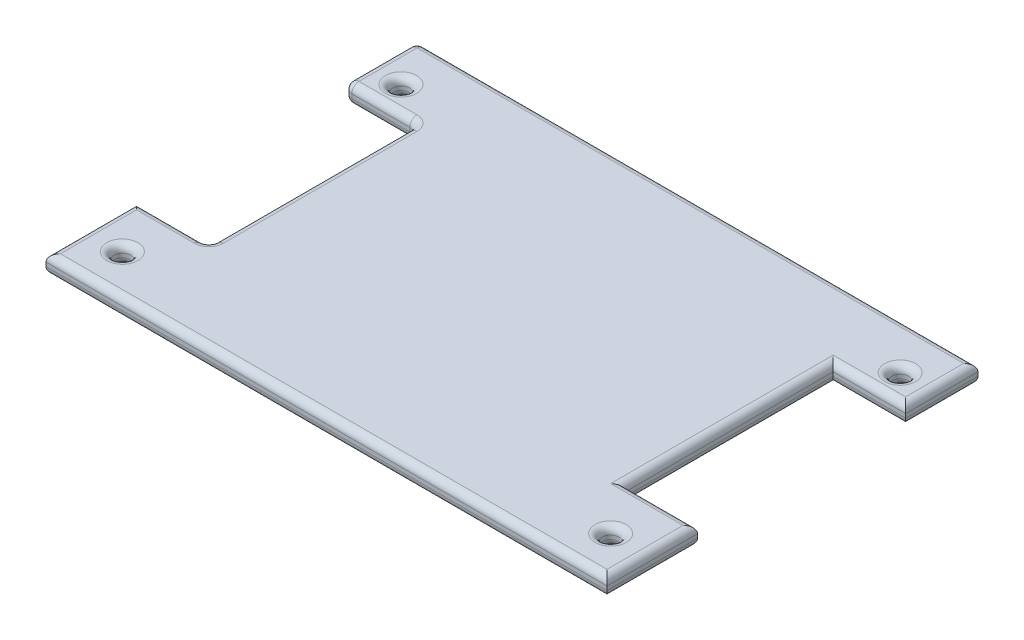
SolidWorks part; units mm, degrees
ref_plane "Front Plane" through (0, 0, 0) normal (0, 0, 1) x (1, 0, 0)
ref_plane "Top Plane" through (0, 0, 0) normal (0, 1, 0) x (1, 0, 0)
ref_plane "Right Plane" through (0, 0, 0) normal (1, 0, 0) x (0, 0, -1)
sketch "Sketch1" plane through (0, 0, 0) normal (0, 1, 0) x (1, 0, 0)
  line L0 (77.5, 0) -> (-77.5, 0)
  line L1 (0, 0) -> (0, 102.5)
  line L2 (77.5, 102.5) -> (-77.5, 102.5)
  line L3 (-77.5, 102.5) -> (-77.5, 82.5)
  line L4 (-77.5, 82.5) -> (-57.5, 82.5)
  line L5 (-57.5, 82.5) -> (-57.5, 25)
  line L6 (-57.5, 25) -> (-77.5, 25)
  line L7 (-77.5, 25) -> (-77.5, 0)
  line L8 (77.5, 25) -> (77.5, 0)
  line L9 (57.5, 25) -> (77.5, 25)
  line L10 (57.5, 82.5) -> (57.5, 25)
  line L11 (77.5, 82.5) -> (57.5, 82.5)
  line L12 (77.5, 102.5) -> (77.5, 82.5)
  dimension "D1" = 77.5
  dimension "D2" = 20
  dimension "D3" = 25
  dimension "D4" = 57.5
  dimension "D5" = 20
  dimension "20" = 20
extrude "Boss-Extrude1" add sketch "Sketch1" along normal blind 5.08 contours L6 L7 L0 L1 L2 L3 L4 L5 | L12 L2 L1 L0 L8 L9 L10 L11
sketch "Sketch2" plane through (0, 5.08, 0) normal (0, 1, 0) x (1, 0, 0)
  line L0 (-77.5, 102.5) -> (-77.5, 82.5) construction
  line L1 (77.5, 0) -> (-77.5, 0) construction
  line L2 (77.5, 102.5) -> (77.5, 82.5) construction
  line L3 (-77.5, 25) -> (-77.5, 0) construction
  line L4 (77.5, 25) -> (77.5, 0) construction
  circle A0 centre (-68.95, 89.55) radius 2.3
  circle A1 centre (68.95, 89.55) radius 2.3
  circle A2 centre (-67.45, 11.05) radius 2.3
  circle A3 centre (67.45, 11.05) radius 2.3
  dimension "D3" = 4.6
  dimension "D4" = 4.6
  dimension "D7" = 4.6
  dimension "D8" = 4.6
  dimension "D1" = 8.55
  dimension "D2" = 89.55
  dimension "D5" = 8.55
  dimension "D6" = 89.55
  dimension "D9" = 11.05
  dimension "D10" = 10.05
  dimension "D11" = 10.05
  dimension "D12" = 11.05
extrude "Cut-Extrude1" cut sketch "Sketch2" against normal up to surface (5.08 mm away) up to face at (0, 0, -52.9167)
fillet "Fillet1" radius 2 36 edges at (-77.5, 0, -12.5) (0, 0, 0) (77.5, 0, -12.5) (67.5, 0, -25) (57.5, 0, -53.75) (67.5, 0, -82.5) (77.5, 0, -92.5) (0, 0, -102.5) (-67.5, 0, -82.5) (-67.5, 0, -25) (-68.95, 0, -87.25) (67.45, 0, -8.75) (-67.45, 0, -8.75) (68.95, 0, -87.25) (-67.5, 5.08, -82.5) (0, 5.08, -102.5) (77.5, 5.08, -92.5) (67.5, 5.08, -82.5) (57.5, 5.08, -53.75) (67.5, 5.08, -25) (77.5, 5.08, -12.5) (0, 5.08, 0) (-77.5, 5.08, -12.5) (-67.5, 5.08, -25) (-68.95, 5.08, -87.25) (67.45, 5.08, -8.75) (-67.45, 5.08, -8.75) (68.95, 5.08, -87.25) (-77.5, 2.54, -102.5) (-77.5, 5.08, -92.5) (-77.5, 2.54, -82.5) (-77.5, 0, -92.5) (-57.5, 2.54, -82.5) (-57.5, 5.08, -53.75) (-57.5, 2.54, -25) (-57.5, 0, -53.75)
